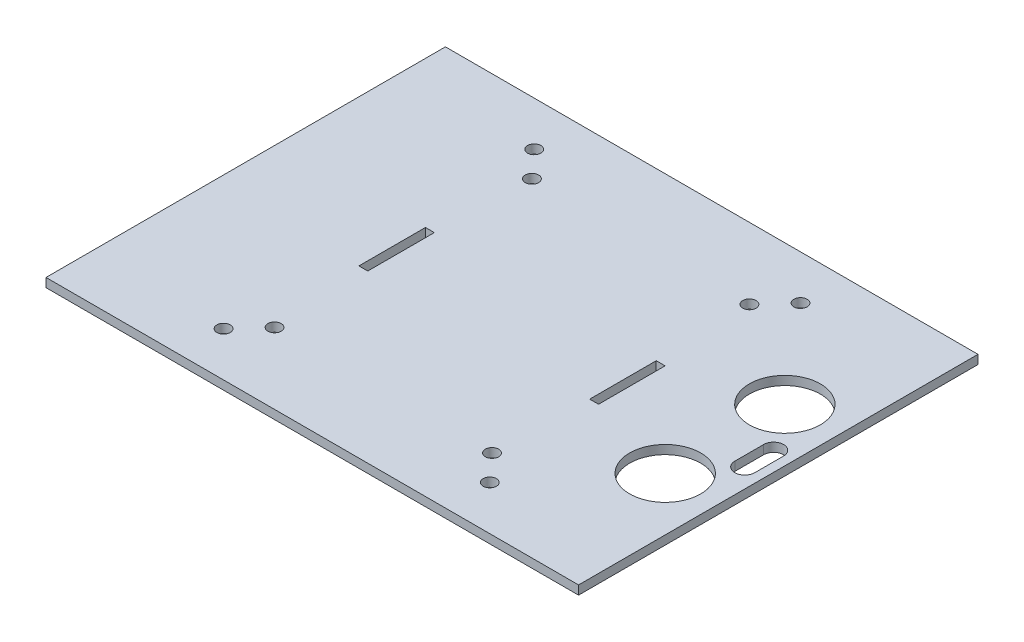
SolidWorks part; units mm, degrees
ref_plane "前基準面" through (0, 0, 0) normal (0, 0, 1) x (1, 0, 0)
ref_plane "上基準面" through (0, 0, 0) normal (0, 1, 0) x (1, 0, 0)
ref_plane "右基準面" through (0, 0, 0) normal (1, 0, 0) x (0, 0, -1)
sketch "草圖1" plane through (0, 0, 0) normal (0, 1, 0) x (1, 0, 0)
  line L0 (27, 0) -> (25, 0) construction
  line L1 (-60, -45) -> (60, -45)
  line L2 (-60, -45) -> (-60, 45)
  line L3 (-60, 45) -> (60, 45)
  line L4 (60, -45) -> (60, 45)
  line L5 (-69.2627, 0) -> (69.2627, 0) construction
  line L6 (0, 45) -> (0, -45) construction
  line L7 (-28, -42.5) -> (28, -42.5) construction
  line L8 (-28, -42.5) -> (-28, 42.5) construction
  line L9 (-28, 42.5) -> (28, 42.5) construction
  line L10 (28, -42.5) -> (28, 42.5) construction
  line L11 (0, 42.5) -> (0, -42.5) construction
  line L12 (-28, 0) -> (28, 0) construction
  line L13 (-27, -7.5) -> (-25, -7.5)
  line L14 (-27, -7.5) -> (-27, 7.5)
  line L15 (-27, 7.5) -> (-25, 7.5)
  line L16 (-25, -7.5) -> (-25, 7.5)
  line L17 (-26, 7.5) -> (-26, -7.5) construction
  line L18 (-27, 0) -> (-25, 0) construction
  line L19 (26, 7.5) -> (26, -7.5) construction
  line L20 (25, -7.5) -> (25, 7.5)
  line L21 (27, 7.5) -> (25, 7.5)
  line L22 (27, -7.5) -> (27, 7.5)
  line L23 (27, -7.5) -> (25, -7.5)
  circle A0 centre (-30, 35) radius 1.5
  circle A1 centre (30, 35) radius 1.5
  circle A2 centre (30, -35) radius 1.5
  circle A3 centre (-30, -35) radius 1.5
  circle A4 centre (24.5, 29) radius 1.5
  circle A5 centre (24.5, -29) radius 1.5
  circle A6 centre (-24.5, 29) radius 1.5
  circle A7 centre (-24.5, -29) radius 1.5
  point P0 (0, 0)
  point P15 (0, 0)
  point P26 (-26, 0)
  point P42 (26, 0)
  point P57 (0, 0)
  dimension "D1" = 3
  dimension "D7" = 3
  dimension "D2" = 70
  dimension "D3" = 60
  dimension "D4" = 85
  dimension "D5" = 56
  dimension "D8" = 49
  dimension "D9" = 58
  dimension "D10" = 90
  dimension "D11" = 120
  dimension "D12" = 50
  dimension "D13" = 15
  dimension "D14" = 2
extrude "填料-伸長1" add sketch "草圖1" along normal blind 2
sketch "草圖2" plane through (0, 2, 0) normal (0, 1, 0) x (1, 0, 0)
  line L0 (-98.9686, 0) -> (98.9686, 0) construction
  line L1 (55.7, -3.25) -> (55.7, 3.25) construction
  line L2 (53.45, -3.25) -> (53.45, 3.25)
  line L3 (57.95, -3.25) -> (57.95, 3.25)
  line L5 (58.35, 22.25) -> (37.65, 22.25) construction
  line L6 (58.35, 22.25) -> (58.35, -22.25) construction
  line L7 (58.35, -22.25) -> (37.65, -22.25) construction
  line L8 (37.65, 22.25) -> (37.65, -22.25) construction
  line L9 (48, -22.25) -> (48, 22.25) construction
  line L10 (58.35, 0) -> (37.65, 0) construction
  circle A0 centre (48, 13.48) radius 8
  circle A1 centre (48, -13.48) radius 8
  arc A2 (53.45, -3.25) -> (57.95, -3.25) centre (55.7, -3.25) ccw
  arc A3 (57.95, 3.25) -> (53.45, 3.25) centre (55.7, 3.25) ccw
  point P4 (0, 0)
  point P10 (55.7, 0)
  point P15 (48, 0)
  dimension "D2" = 16
  dimension "D1" = 26.96
  dimension "D3" = 20.7
  dimension "D4" = 0.4
  dimension "D5" = 6.5
  dimension "D6" = 4.5
  dimension "D7" = 44.5
  dimension "D8" = 48
extrude "除料-伸長1" cut sketch "草圖2" against normal through all
